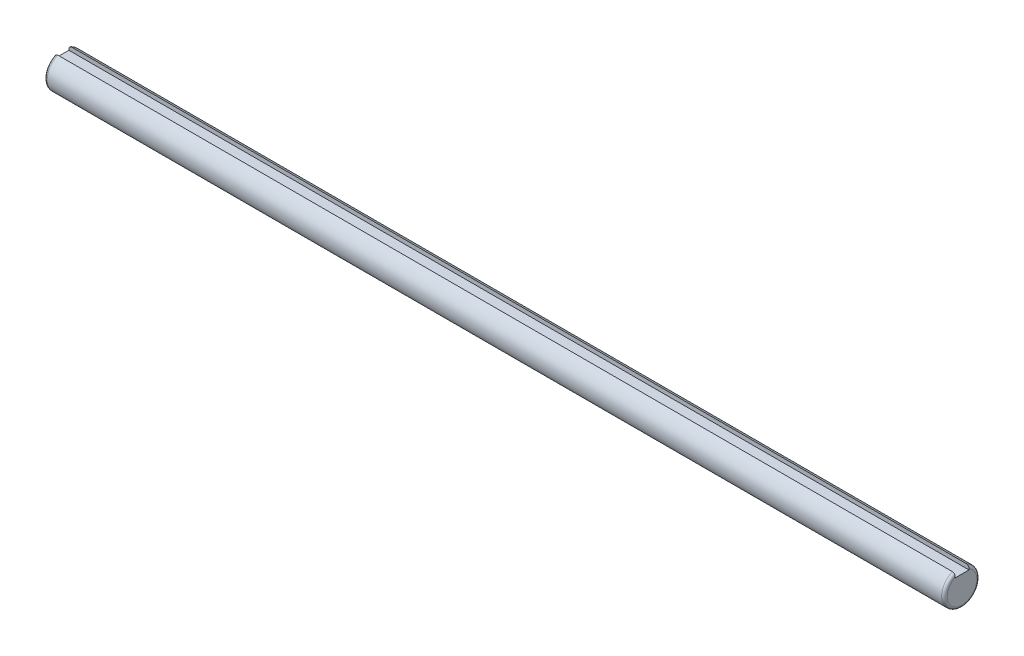
SolidWorks part; units mm, degrees
ref_plane "Front Plane" through (0, 0, 0) normal (0, 0, 1) x (1, 0, 0)
ref_plane "Top Plane" through (0, 0, 0) normal (0, 1, 0) x (1, 0, 0)
ref_plane "Right Plane" through (0, 0, 0) normal (1, 0, 0) x (0, 0, -1)
sketch "Sketch2" plane through (0, 0, 0) normal (1, 0, 0) x (0, 0, -1)
  line L2 (2.5, 5.8372) -> (2.5, 4.35)
  line L3 (2.5, 4.35) -> (-2.5, 4.35)
  line L4 (-2.5, 5.8372) -> (-2.5, 4.35)
  arc A0 (-2.5, 5.8372) -> (2.5, 5.8372) centre (0, 0) ccw
  point P3 (0, 6.35)
  dimension "D1" = 12.7
  dimension "D2" = 5
extrude "Boss-Extrude1" add sketch "Sketch2" along normal blind 325
fillet "Fillet1" radius 1 2 edges at (0, -6.35, 0) (325, -6.35, 0)
